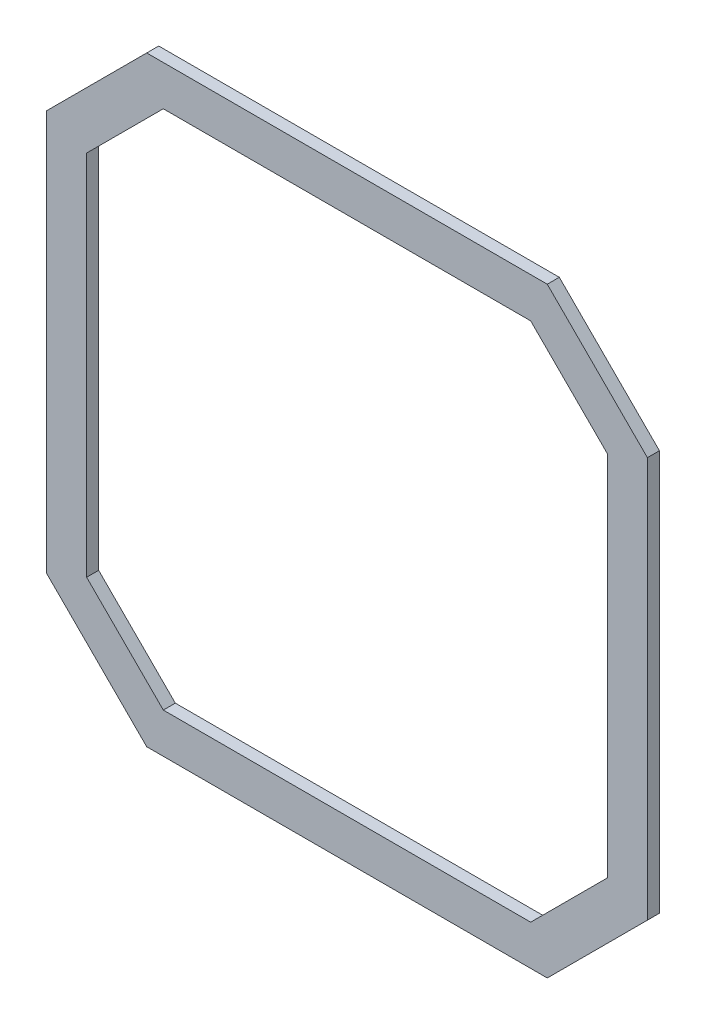
SolidWorks part; units mm, degrees
ref_plane "Front Plane" through (0, 0, 0) normal (0, 0, 1) x (1, 0, 0)
ref_plane "Top Plane" through (0, 0, 0) normal (0, 1, 0) x (1, 0, 0)
ref_plane "Right Plane" through (0, 0, 0) normal (1, 0, 0) x (0, 0, -1)
sketch "Sketch1" plane through (0, 0, 0) normal (0, 0, 1) x (1, 0, 0)
  line L0 (45.5, 78.6673) -> (70.5, 53.6673)
  line L1 (-54.5, 78.6673) -> (45.5, 78.6673)
  line L2 (-79.5, 53.6673) -> (-79.5, -46.3327)
  line L3 (-54.5, -71.3327) -> (45.5, -71.3327)
  line L4 (70.5, 53.6673) -> (70.5, -46.3327)
  line L5 (-79.5, 3.6673) -> (79.5, 3.6673) construction
  line L7 (-54.5, 78.6673) -> (-79.5, 53.6673)
  line L8 (-54.5, -71.3327) -> (-79.5, -46.3327)
  line L9 (45.5, -71.3327) -> (70.5, -46.3327)
  line L10 (41.3579, 68.6673) -> (60.5, 49.5252)
  line L11 (60.5, 49.5252) -> (60.5, -42.1906)
  line L12 (41.3579, -61.3327) -> (60.5, -42.1906)
  line L13 (-50.3579, -61.3327) -> (41.3579, -61.3327)
  line L14 (-50.3579, -61.3327) -> (-69.5, -42.1906)
  line L15 (-69.5, 49.5252) -> (-69.5, -42.1906)
  line L16 (-50.3579, 68.6673) -> (-69.5, 49.5252)
  line L17 (-50.3579, 68.6673) -> (41.3579, 68.6673)
  line L18 (-54.5, 78.6673) -> (45.5, 78.6673) construction
  line L19 (-54.5, -71.3327) -> (45.5, -71.3327) construction
  point P21 (-79.5, 10)
  point P22 (79.5, 10)
  point P23 (10, 75)
  point P24 (10, -75)
  dimension "D1" = 10
  dimension "D2" = 100
  dimension "D3" = 135
  dimension "D4" = 100
  dimension "D5" = 100
  dimension "D6" = 150
  dimension "D7" = 150
extrude "Boss-Extrude1" add sketch "Sketch1" along normal blind 3
